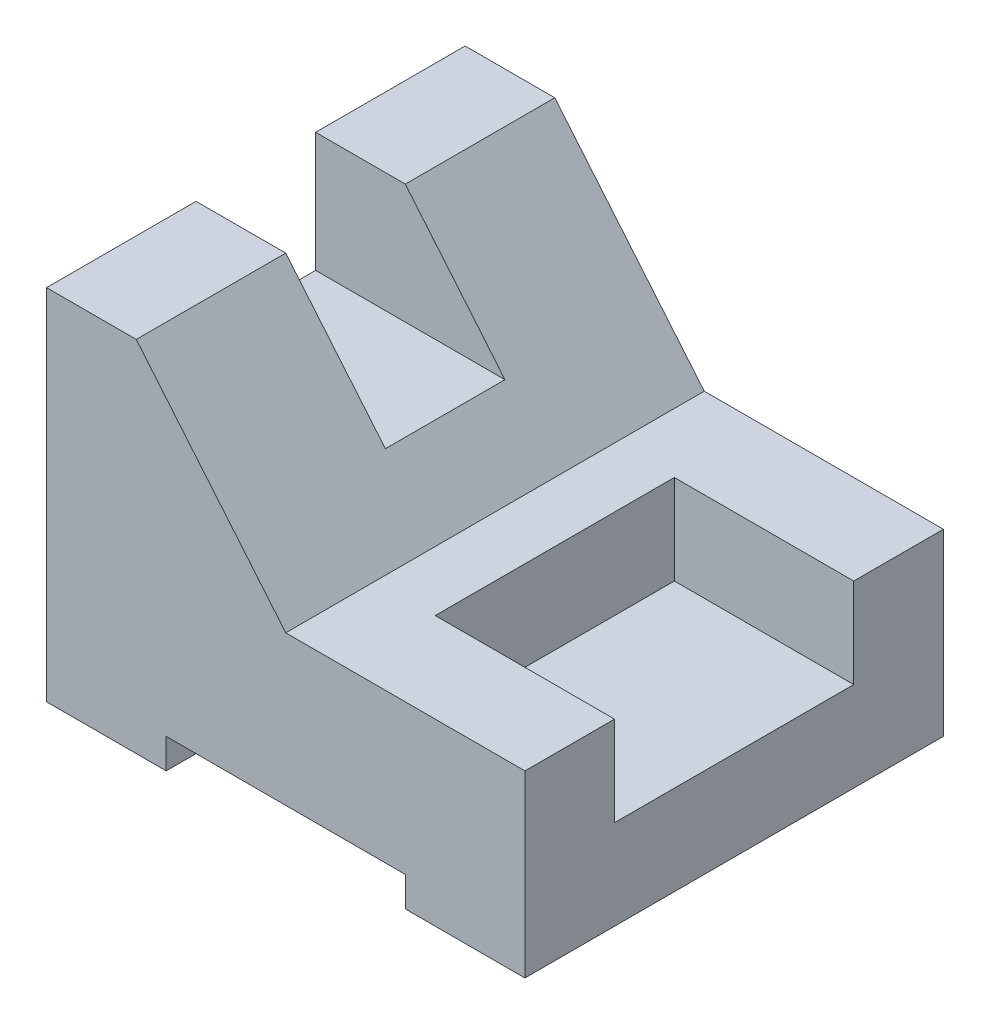
SolidWorks part; units mm, degrees
ref_plane "Front Plane" through (0, 0, 0) normal (0, 0, 1) x (1, 0, 0)
ref_plane "Top Plane" through (0, 0, 0) normal (0, 1, 0) x (1, 0, 0)
ref_plane "Right Plane" through (0, 0, 0) normal (1, 0, 0) x (0, 0, -1)
sketch "Sketch1" plane through (0, 0, 0) normal (0, 0, 1) x (1, 0, 0)
  line L0 (0, 0) -> (0, 60)
  line L1 (0, 60) -> (15, 60)
  line L2 (0, 0) -> (20, 0)
  line L3 (20, 0) -> (20, 5)
  line L4 (20, 5) -> (60, 5)
  line L5 (60, 5) -> (60, 0)
  line L6 (60, 0) -> (80, 0)
  line L7 (80, 0) -> (80, 30)
  line L8 (80, 30) -> (40, 30)
  line L9 (40, 30) -> (15, 60)
  dimension "D1" = 60
  dimension "D2" = 15
  dimension "D3" = 5
  dimension "D4" = 40
  dimension "D5" = 20
  dimension "D6" = 39.0512
  dimension "D7" = 40
  dimension "D8" = 30
extrude "Boss-Extrude1" add sketch "Sketch1" along normal mid plane 70
sketch "Sketch2" plane through (0, 0, 0) normal (0, 0, 1) x (1, 0, 0)
  line L0 (15, 60) -> (0, 60)
  line L1 (15, 60) -> (0, 60) construction
  line L2 (0, 60) -> (0, 40)
  line L3 (0, 60) -> (0, 0) construction
  line L4 (0, 40) -> (31.6667, 40)
  line L5 (40, 30) -> (15, 60) construction
  line L6 (31.6667, 40) -> (15, 60)
  dimension "D1" = 20
  dimension "D2" = 31.6667
extrude "Cut-Extrude1" cut sketch "Sketch2" against normal mid plane 20 contours L6 L0 L2 L4
sketch "Sketch3" plane through (0, 0, 0) normal (0, 0, 1) x (1, 0, 0)
  line L0 (80, 30) -> (80, 15)
  line L1 (80, 0) -> (80, 30) construction
  line L2 (80, 15) -> (50, 15)
  line L3 (50, 15) -> (50, 30)
  line L4 (80, 30) -> (40, 30) construction
  line L5 (50, 30) -> (80, 30)
  dimension "D1" = 30
extrude "Cut-Extrude2" cut sketch "Sketch3" against normal mid plane 40 contours L5 L0 L2 L3
